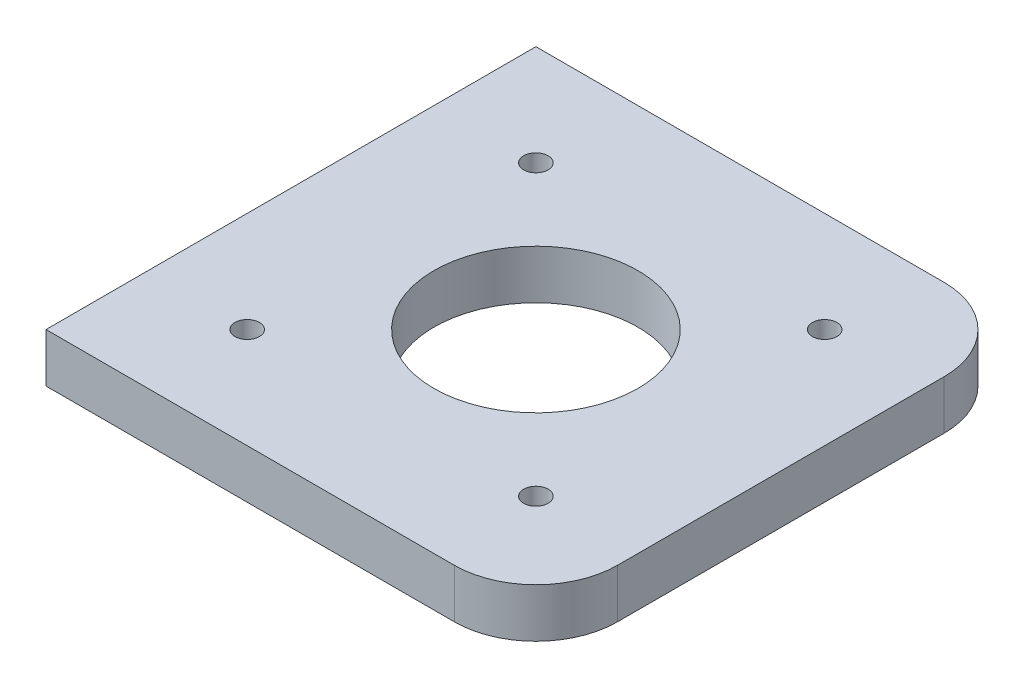
SolidWorks part; units mm, degrees
ref_plane "Front Plane" through (0, 0, 0) normal (0, 0, 1) x (1, 0, 0)
ref_plane "Top Plane" through (0, 0, 0) normal (0, 1, 0) x (1, 0, 0)
ref_plane "Right Plane" through (0, 0, 0) normal (1, 0, 0) x (0, 0, -1)
sketch "Sketch1" plane through (0, 0, 0) normal (0, 1, 0) x (1, 0, 0)
  line L0 (-12.32, 47.68) -> (47.68, -12.32) construction
  line L1 (0, 0) -> (35.36, 0) construction
  line L2 (0, 0) -> (0, 35.36) construction
  line L3 (0, 35.36) -> (35.36, 35.36) construction
  line L4 (35.36, 0) -> (35.36, 35.36) construction
  line L5 (-12.32, 47.68) -> (47.68, 47.68)
  line L6 (-12.32, 47.68) -> (-12.32, -12.32)
  line L7 (-12.32, -12.32) -> (47.68, -12.32)
  line L8 (47.68, 47.68) -> (47.68, -12.32)
  line L9 (-12.32, -12.32) -> (47.68, 47.68) construction
  line L10 (0, 35.36) -> (35.36, 0) construction
  line L11 (35.36, 35.36) -> (0, 0) construction
  circle A0 centre (0, 35.36) radius 1.5
  circle A1 centre (35.36, 35.36) radius 1.5
  circle A2 centre (35.36, 0) radius 1.5
  circle A3 centre (0, 0) radius 1.5
  circle A4 centre (17.68, 17.68) radius 12.5
  point P13 (17.68, 17.68)
  point P14 (17.68, 17.68)
  dimension "D3" = 3
  dimension "D4" = 3
  dimension "D5" = 3
  dimension "D6" = 3
  dimension "D9" = 25
  dimension "D1" = 35.36
  dimension "D2" = 35.36
  dimension "D7" = 60
  dimension "D8" = 60
extrude "Boss-Extrude1" add sketch "Sketch1" along normal blind 6
fillet "Fillet1" radius 10 2 edges at (47.68, 3, -47.68) (47.68, 3, 12.32)
scale "Scale2" scale about centroid uniform scaling yes scale factor 7.5
